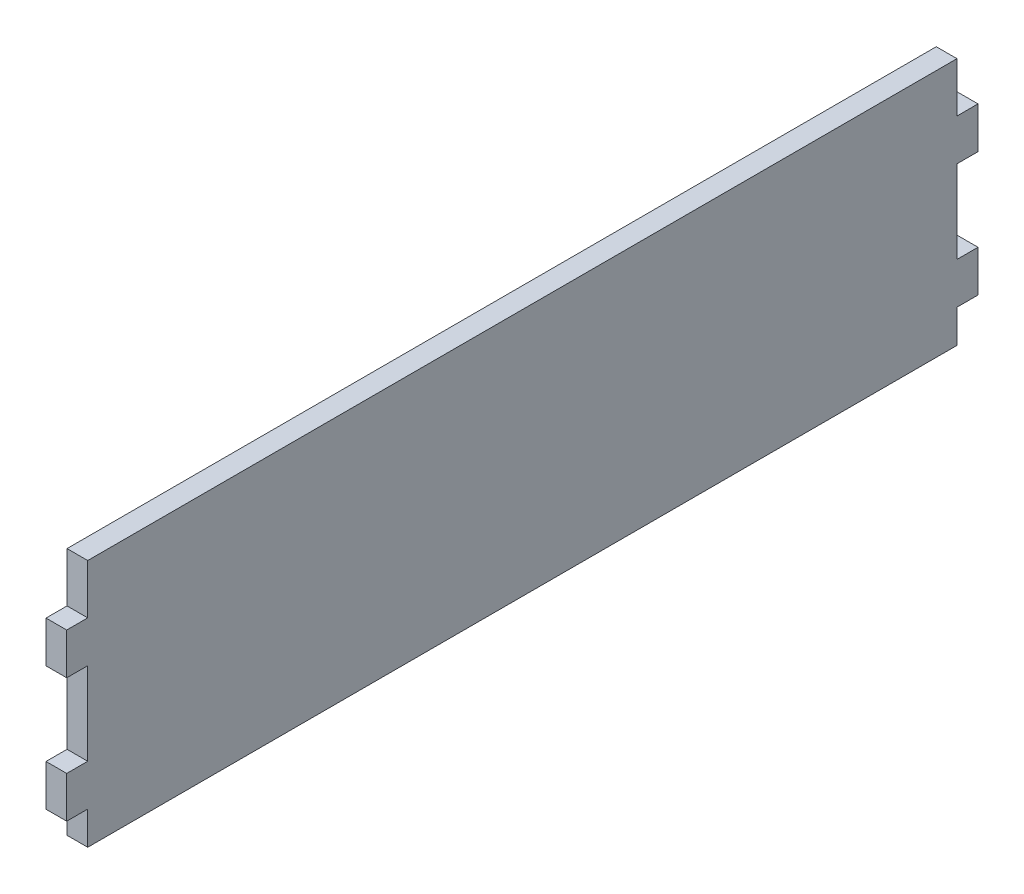
SolidWorks part; units mm, degrees
ref_plane "Front Plane" through (0, 0, 0) normal (0, 0, 1) x (1, 0, 0)
ref_plane "Top Plane" through (0, 0, 0) normal (0, 1, 0) x (1, 0, 0)
ref_plane "Right Plane" through (0, 0, 0) normal (1, 0, 0) x (0, 0, -1)
sketch "Sketch1" plane through (0, 0, 0) normal (1, 0, 0) x (0, 0, -1)
  line L1 (-66.675, -19.05) -> (66.675, -19.05)
  line L2 (-66.675, -19.05) -> (-66.675, 19.05)
  line L3 (-66.675, 19.05) -> (66.675, 19.05)
  line L4 (66.675, -19.05) -> (66.675, 19.05)
  line L5 (-66.675, -19.05) -> (66.675, 19.05) construction
  line L6 (-66.675, 19.05) -> (66.675, -19.05) construction
  point P0 (0, 0)
  dimension "D1" = 133.35
  dimension "D2" = 38.1
extrude "Boss-Extrude1" add sketch "Sketch1" along normal blind 3.175
sketch "Sketch2" plane through (0, 0, 0) normal (-1, 0, 0) x (0, 0, 1)
  line L0 (-66.675, 11.43) -> (-69.9008, 11.43)
  line L1 (-66.675, -19.05) -> (-66.675, 19.05) construction
  line L2 (-69.9008, 11.43) -> (-69.9008, 5.08)
  line L3 (-69.9008, 5.08) -> (-66.675, 5.08)
  line L4 (-66.675, 5.08) -> (-66.675, 11.43)
  line L5 (-66.675, -7.62) -> (-69.9008, -7.62)
  line L6 (-69.9008, -7.62) -> (-69.9008, -13.97)
  line L7 (-69.9008, -13.97) -> (-66.675, -13.97)
  line L8 (-66.675, -13.97) -> (-66.675, -7.62)
  line L9 (66.675, -19.05) -> (-66.675, -19.05) construction
  point P13 (-70.9556, -1.4663)
  dimension "D1" = 3.2258
  dimension "D2" = 6.35
  dimension "D3" = 6.35
  dimension "D4" = 3.2258
  dimension "D5" = 5.08
  dimension "D6" = 12.7
extrude "Boss-Extrude2" add sketch "Sketch2" against normal blind 3.175
mirror "Mirror1" about plane through (0, 0, 0) normal (0, 0, 1) of "Boss-Extrude2"
